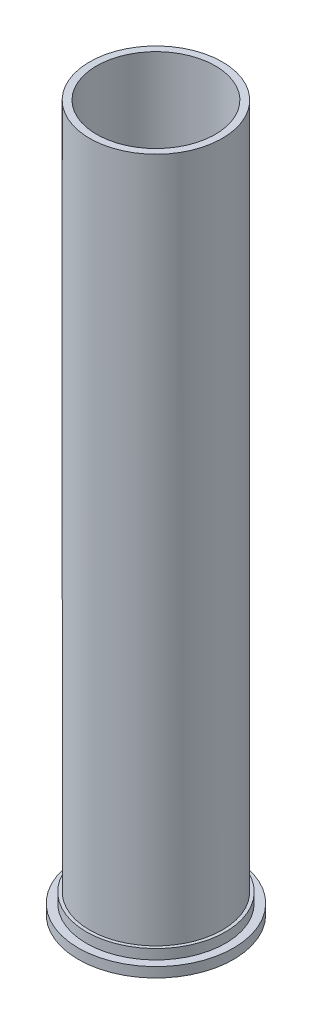
SolidWorks part; units mm, degrees
ref_plane "Front Plane" through (0, 0, 0) normal (0, 0, 1) x (1, 0, 0)
ref_plane "Top Plane" through (0, 0, 0) normal (0, 1, 0) x (1, 0, 0)
ref_plane "Right Plane" through (0, 0, 0) normal (1, 0, 0) x (0, 0, -1)
sketch "Sketch1" plane through (0, 0, 0) normal (0, 0, 1) x (1, 0, 0)
  line L0 (0, 0) -> (0, 10.0982) construction
  line L1 (12.815, 0) -> (14.315, 0)
  line L2 (14.315, 0) -> (14.315, 152.24)
  line L3 (14.315, 152.24) -> (12.815, 152.24)
  line L4 (12.815, 152.24) -> (12.815, 0)
  dimension "D1" = 1.5
  dimension "D2" = 152.24
  dimension "D3" = 14.315
revolve "Revolve1" add sketch "Sketch1" angle 360 about L0
sketch "Sketch2" plane through (0, 0, 0) normal (0, 1, 0) x (1, 0, 0)
  circle A1 centre (0, 0) radius 16.75
  dimension "D2" = 33.5
extrude "Boss-Extrude1" add sketch "Sketch2" along normal blind 2.14
sketch "Sketch4" plane through (0, 2.14, 0) normal (0, 1, 0) x (1, 0, 0)
  circle A0 centre (0, 0) radius 15
  dimension "D1" = 30
extrude "Boss-Extrude2" add sketch "Sketch4" along normal blind 2.14
